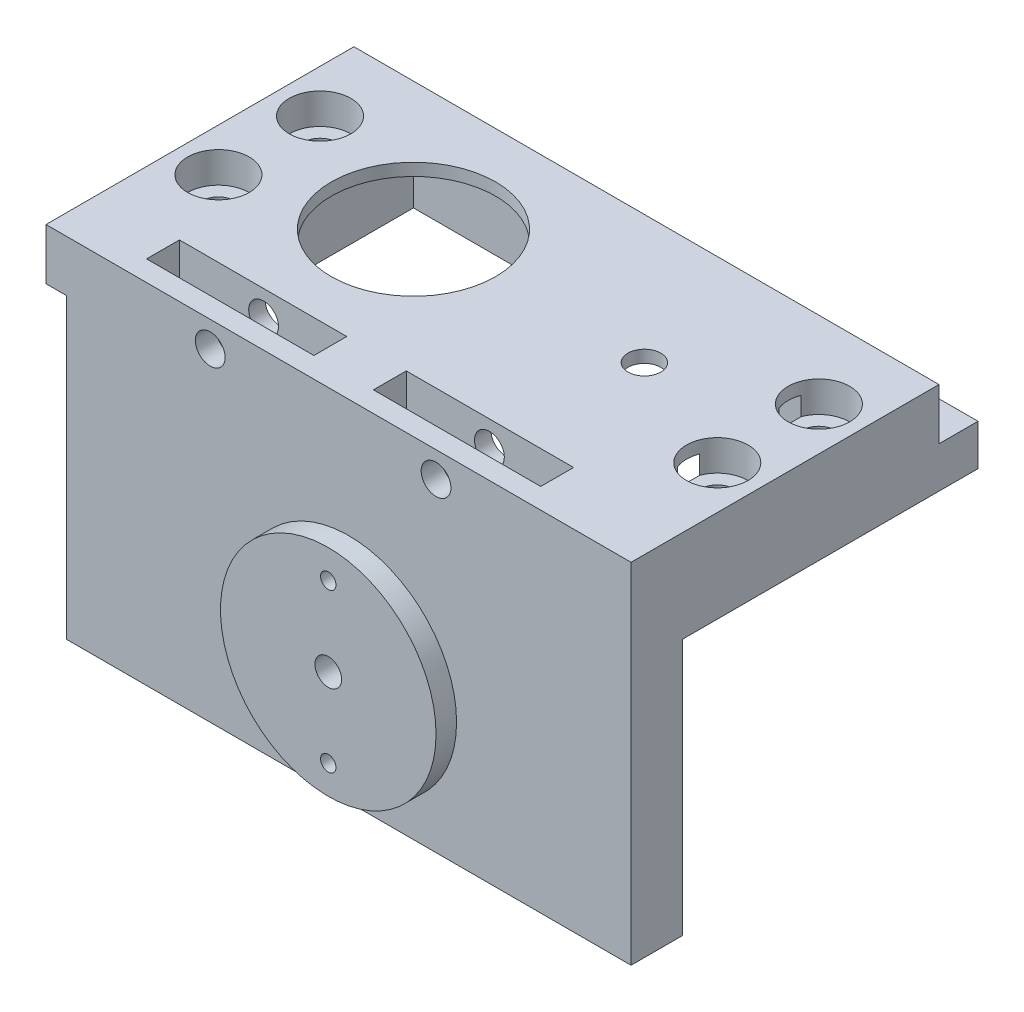
SolidWorks part; units mm, degrees
ref_plane "Front Plane" through (0, 0, 0) normal (0, 0, 1) x (1, 0, 0)
ref_plane "Top Plane" through (0, 0, 0) normal (0, 1, 0) x (1, 0, 0)
ref_plane "Right Plane" through (0, 0, 0) normal (1, 0, 0) x (0, 0, -1)
sketch "Sketch1" plane through (0, 0, 0) normal (0, 1, 0) x (1, 0, 0)
  line L0 (-11.25, 0) -> (11.25, 0)
  line L1 (-25, -12.5) -> (25, -12.5)
  line L2 (-25, -12.5) -> (-25, 12.5)
  line L3 (-25, 12.5) -> (25, 12.5)
  line L4 (25, -12.5) -> (25, 12.5)
  line L5 (-25, -12.5) -> (25, 12.5) construction
  line L6 (-25, 12.5) -> (25, -12.5) construction
  circle A0 centre (-11.25, 0) radius 1.3
  circle A1 centre (11.25, 0) radius 4.5
  point P0 (0, 0)
  point P10 (0, 0)
  dimension "D3" = 2.6
  dimension "D4" = 9
  dimension "D1" = 25
  dimension "D2" = 50
  dimension "D5" = 22.5
extrude "Boss-Extrude1" add sketch "Sketch1" along normal mid plane 5
sketch "Sketch2" plane through (0, 0, 12.5) normal (0, 0, 1) x (1, 0, 0)
  line L0 (-25, 2.5) -> (-25, -2.5) construction
  line L1 (-25, -2.5) -> (25, -2.5)
  line L2 (-25, -2.5) -> (-25, 9.5)
  line L3 (-25, 9.5) -> (25, 9.5)
  line L4 (25, -2.5) -> (25, 9.5)
  line L5 (-25, -2.5) -> (25, -2.5) construction
  dimension "D1" = 50
  dimension "D2" = 12
extrude "Boss-Extrude2" add sketch "Sketch2" along normal blind 3
sketch "Sketch3" plane through (0, 9.5, 0) normal (0, 1, 0) x (1, 0, 0)
  line L0 (-25, -15.5) -> (-25, -12.5) construction
  line L1 (-25, -15.5) -> (25, -15.5)
  line L2 (-25, -15.5) -> (-25, 12.5)
  line L3 (-25, 12.5) -> (25, 12.5)
  line L4 (25, -15.5) -> (25, 12.5)
  line L5 (-25, 12.5) -> (25, 12.5) construction
extrude "Boss-Extrude3" add sketch "Sketch3" along normal blind 3
sketch "Sketch4" plane through (0, 12.5, 0) normal (0, 1, 0) x (1, 0, 0)
  line L0 (11.25, 0) -> (-11.25, 0)
  line L1 (-25, 12.5) -> (25, 12.5) construction
  line L2 (-25, -15.5) -> (-25, 12.5) construction
  circle A0 centre (11.25, 0) radius 1.3
  circle A1 centre (-11.25, 0) radius 1.3
  dimension "D1" = 2.6
  dimension "D2" = 2.6
  dimension "D3" = 11.25
  dimension "D4" = 12.5
  dimension "D5" = 13.75
extrude "Cut-Extrude1" cut sketch "Sketch4" against normal through all
sketch "Sketch5" plane through (0, -2.5, 0) normal (0, -1, 0) x (1, 0, 0)
  line L11 (21.45, -10.3) -> (21.45, 10.2) construction
  line L20 (0.95, 10.2) -> (41.95, 10.2) construction
  line L21 (0.95, 10.2) -> (0.95, -10.3) construction
  line L22 (0.95, -10.3) -> (41.95, -10.3) construction
  line L23 (41.95, 10.2) -> (41.95, -10.3) construction
  line L24 (-5.05, 16.2) -> (47.95, 16.2)
  line L25 (47.95, 16.2) -> (47.95, -16.3)
  line L26 (-5.05, -16.3) -> (47.95, -16.3)
  line L27 (-5.05, 16.2) -> (-5.05, -16.3)
  line L28 (0.45, 10.7) -> (42.45, 10.7)
  line L29 (42.45, 10.7) -> (42.45, -10.8)
  line L30 (0.45, -10.8) -> (42.45, -10.8)
  line L31 (0.45, 10.7) -> (0.45, -10.8)
  circle A5 centre (11.25, 0) radius 7.5 construction
  circle A6 centre (45.75, -5) radius 1.6
  circle A7 centre (45.75, 4.9) radius 1.6
  circle A8 centre (-2.85, 4.9) radius 1.6
  circle A9 centre (-2.85, -5) radius 1.6
  dimension "D4" = 10.3
  dimension "D5" = 10.3
  dimension "D8" = 3.8
  dimension "D9" = 5.3
  dimension "D1" = 15
  dimension "D6" = 3.2
  dimension "D7" = 3.2
  dimension "D2" = 41
  dimension "D3" = 20.5
  dimension "D10" = 5.3
  dimension "D11" = 6
  dimension "D12" = 0.5
extrude "Boss-Extrude4" add sketch "Sketch5" along normal blind 4
sketch "Sketch7" plane through (0, -2.5, 0) normal (0, -1, 0) x (1, 0, 0)
  circle A0 centre (11.25, 0) radius 8
  dimension "D1" = 16
extrude "Cut-Extrude2" cut sketch "Sketch7" against normal up to surface (5 mm away) up to face at (11.25, 2.5, 4.5)
sketch "Sketch8" plane through (0, -2.5, 0) normal (0, -1, 0) x (1, 0, 0)
  line L4 (0.45, 10.7) -> (0.45, -10.8)
  line L5 (0.45, 10.7) -> (0.45, -10.8)
  line L6 (0.45, -10.8) -> (25, -10.8)
  line L7 (25, -10.8) -> (25, 10.7)
  line L11 (25, -10.8) -> (25, 10.7)
  line L12 (0.45, -10.8) -> (25, -10.8)
  line L13 (25, 10.7) -> (0.45, 10.7)
  line L14 (25, 10.7) -> (0.45, 10.7)
  dimension "D1" = 0
extrude "Cut-Extrude3" cut sketch "Sketch8" against normal blind 3.8
sketch "Sketch9" plane through (25, 0, 0) normal (1, 0, 0) x (0, 0, -1)
  line L0 (-12.5, 2.5) -> (-15.5, 2.5)
  line L1 (-15.5, 2.5) -> (-16.2, 2.5)
  line L2 (-16.2, 2.5) -> (-16.2, -2.5)
  line L3 (-16.2, -2.5) -> (-15.5, -2.5)
  line L12 (-10.7, 1.3) -> (10.8, 1.3)
  line L13 (-10.7, -2.5) -> (-10.7, 1.3)
  line L14 (10.8, -2.5) -> (12.5, -2.5)
  line L15 (12.5, -2.5) -> (12.5, 2.5)
  line L16 (12.5, 2.5) -> (-12.5, 2.5)
  line L17 (-12.5, 2.5) -> (-12.5, 9.5)
  line L18 (-12.5, 9.5) -> (12.5, 9.5)
  line L19 (12.5, 9.5) -> (12.5, 12.5)
  line L20 (12.5, 12.5) -> (-15.5, 12.5)
  line L21 (-15.5, 12.5) -> (-15.5, -2.5)
  line L22 (-15.5, -2.5) -> (-10.7, -2.5)
  line L23 (-10.7, -2.5) -> (-10.7, 1.3)
  line L24 (-10.7, 1.3) -> (10.8, 1.3)
  line L26 (10.8, -2.5) -> (12.5, -2.5)
  line L27 (12.5, -2.5) -> (12.5, 2.5)
  line L28 (12.5, 2.5) -> (-12.5, 2.5)
  line L29 (-12.5, 2.5) -> (-12.5, 9.5)
  line L30 (-12.5, 9.5) -> (12.5, 9.5)
  line L31 (12.5, 9.5) -> (12.5, 12.5)
  line L32 (12.5, 12.5) -> (-15.5, 12.5)
  line L33 (-15.5, 12.5) -> (-15.5, -2.5)
  line L34 (-15.5, -2.5) -> (-10.7, -2.5)
  line L40 (10.8, 1.3) -> (10.8, -2.5)
  line L41 (10.8, 1.3) -> (10.8, -2.5)
  dimension "D1" = 0
extrude "Boss-Extrude6" add sketch "Sketch9" along normal up to surface (22.95 mm away) up to face at (47.95, -4.5, -0.05)
sketch "Sketch10" plane through (47.95, 0, 0) normal (1, 0, 0) x (0, 0, -1)
  line L6 (16.3, -2.5) -> (12.5, -2.5)
  line L7 (12.5, -2.5) -> (12.5, 2.5)
  line L8 (12.5, 2.5) -> (-16.2, 2.5)
  line L9 (-16.2, 2.5) -> (-16.2, -6.5)
  line L10 (-16.2, -6.5) -> (16.3, -6.5)
  line L11 (16.3, -6.5) -> (16.3, -2.5)
  line L12 (16.3, -2.5) -> (12.5, -2.5)
  line L13 (12.5, -2.5) -> (12.5, 2.5)
  line L14 (12.5, 2.5) -> (-16.2, 2.5)
  line L15 (-16.2, 2.5) -> (-16.2, -6.5)
  line L16 (-16.2, -6.5) -> (16.3, -6.5)
  line L17 (16.3, -6.5) -> (16.3, -2.5)
  dimension "D1" = 0
extrude "Boss-Extrude7" add sketch "Sketch10" along normal blind 2
sketch "Sketch11" plane through (0, 1.3, 0) normal (0, -1, 0) x (1, 0, 0)
  circle A0 centre (-2.85, 4.9) radius 1.6 construction
  circle A1 centre (-2.85, -5) radius 1.6 construction
  circle A2 centre (45.75, 4.9) radius 1.6 construction
  circle A3 centre (45.75, -5) radius 1.6 construction
  circle A4 centre (-2.85, 4.9) radius 1.6
  circle A5 centre (-2.85, -5) radius 1.6
  circle A6 centre (45.75, 4.9) radius 1.6
  circle A7 centre (45.75, -5) radius 1.6
extrude "Cut-Extrude4" cut sketch "Sketch11" against normal up to surface (1.2 mm away) up to face at (11.25, 2.5, 8)
sketch "Sketch12" plane through (0, 1.3, 0) normal (0, -1, 0) x (1, 0, 0)
  line L0 (49.95, 16.2) -> (49.95, -16.3) construction
  line L1 (42.95, 10.7) -> (49.95, 10.7)
  line L2 (42.95, 10.7) -> (42.95, -10.3)
  line L3 (42.95, -10.3) -> (49.95, -10.3)
  line L4 (49.95, 10.7) -> (49.95, -10.3)
  line L6 (0.45, 10.7) -> (0.45, -10.8) construction
  line L7 (47.95, 10.7) -> (0.45, 10.7) construction
  line L8 (0.45, 10.7) -> (42.45, 10.7) construction
  circle A0 centre (45.75, 4.9) radius 1.6 construction
  circle A1 centre (45.75, -5) radius 1.6 construction
  circle A2 centre (45.75, 4.9) radius 1.6
  circle A3 centre (45.75, -5) radius 1.6
  dimension "D1" = 42.5
  dimension "D2" = 21
extrude "Boss-Extrude8" add sketch "Sketch12" along normal up to surface (7.8 mm away) up to face at (22.45, -6.5, -0.05)
sketch "Sketch13" plane through (25, 0, 0) normal (-1, 0, 0) x (0, 0, 1)
  line L1 (15.5, 2.5) -> (16.2, 2.5)
  line L2 (15.5, 2.5) -> (15.5, -6.5)
  line L3 (15.5, -6.5) -> (16.2, -6.5)
  line L4 (16.2, 2.5) -> (15.5, 2.5)
  line L5 (15.5, 2.5) -> (15.5, -2.5)
  line L6 (15.5, -2.5) -> (16.2, -2.5)
  line L7 (16.2, -2.5) -> (16.2, 2.5)
  line L8 (16.2, 2.5) -> (15.5, 2.5)
  line L9 (15.5, 2.5) -> (15.5, -2.5)
  line L11 (16.2, -2.5) -> (16.2, 2.5)
  line L12 (16.2, 2.5) -> (16.2, -6.5)
  line M5 (16.2, 2.5) -> (15.5, 2.5)
  line M6 (15.5, 2.5) -> (15.5, -2.5)
  line M7 (15.5, -2.5) -> (16.2, -2.5)
  line M8 (16.2, -2.5) -> (16.2, 2.5)
  dimension "D1" = 0
extrude "Cut-Extrude5" cut sketch "Sketch13" against normal through all both and the other way through all contours M8 M5 M6 M7 | L12 L2 L3 M7
sketch "Sketch14" plane through (-25, 0, 0) normal (-1, 0, 0) x (0, 0, 1)
  line L0 (15.5, 12.5) -> (15.5, -2.5) construction
  line L1 (-12.5, 12.5) -> (15.5, 12.5)
  line L2 (-12.5, 12.5) -> (-12.5, 2.5)
  line L3 (-12.5, 2.5) -> (15.5, 2.5)
  line L4 (15.5, 12.5) -> (15.5, 2.5)
  line L5 (12.5, 2.5) -> (-12.5, 2.5) construction
extrude "Cut-Extrude6" cut sketch "Sketch14" against normal through all both and the other way through all
sketch "Sketch15" plane through (0, 2.5, 0) normal (0, 1, 0) x (1, 0, 0)
  circle A0 centre (-2.85, 5) radius 1.6
  circle A1 centre (-2.85, -4.9) radius 1.6
  dimension "D1" = 3.2
  dimension "D2" = 3.2
sketch "Sketch16" plane through (0, 2.5, 0) normal (0, 1, 0) x (1, 0, 0)
  circle A0 centre (-2.85, 5) radius 3
  circle A1 centre (-2.85, -4.9) radius 3
  circle A2 centre (45.75, 5) radius 3
  circle A3 centre (45.75, -4.9) radius 3
  dimension "D1" = 6
  dimension "D2" = 6
  dimension "D3" = 6
  dimension "D4" = 6
extrude "Cut-Extrude8" cut sketch "Sketch16" against normal blind 3
extrude "Cut-Extrude9" cut sketch "Sketch15" against normal up to surface (5 mm away) up to face at (44.45, -2.5, -3.4667)
sketch "Sketch17" plane through (0, 0, 15.5) normal (0, 0, 1) x (1, 0, 0)
  line L1 (49.95, 2.5) -> (-25, 2.5) construction
  line L2 (-5.05, 2.5) -> (0.75, 2.5)
  line L3 (-5.05, 2.5) -> (-5.05, -2.5)
  line L4 (-5.05, -2.5) -> (0.75, -2.5)
  line L5 (0.75, 2.5) -> (0.75, -2.5)
  line L7 (-5.05, 2.5) -> (44.95, 2.5)
  line L8 (22.85, 2.5) -> (17.05, 2.5)
  line L9 (22.85, 2.5) -> (22.85, -2.5)
  line L10 (22.85, -2.5) -> (17.05, -2.5)
  line L11 (17.05, 2.5) -> (17.05, -2.5)
  line L12 (44.95, 2.5) -> (39.15, 2.5)
  line L13 (44.95, 2.5) -> (44.95, -2.5)
  line L14 (44.95, -2.5) -> (39.15, -2.5)
  line L15 (39.15, 2.5) -> (39.15, -2.5)
  line L16 (44.95, -2.5) -> (-5.05, -2.5)
  line L17 (-5.05, -6.5) -> (-5.05, -2.5) construction
  point P17 (19.95, -2.5)
  point P18 (19.95, -2.5)
  line M14 (49.95, 2.5) -> (-25, 2.5)
  dimension "D1" = 5
  dimension "D2" = 5.8
  dimension "D3" = 5.8
  dimension "D4" = 5.8
  dimension "D5" = 50
extrude "Cut-Extrude10" cut sketch "Sketch17" against normal blind 3.2 contours L16 L11 L5 M14 | L16 L15 L7 L9
sketch "Sketch18" plane through (0, 0, 12.3) normal (0, 0, 1) x (1, 0, 0)
  line L3 (39.15, 2.5) -> (22.85, 2.5) construction
  line L4 (17.05, 2.5) -> (0.75, 2.5) construction
  circle A0 centre (8.95, 0) radius 1.45
  circle A1 centre (30.95, 0) radius 1.45
  dimension "D1" = 2.9
  dimension "D2" = 2.9
  dimension "D3" = 22
  dimension "D4" = 14
  dimension "D5" = 2.5
  dimension "D6" = 2.5
  dimension "D7" = 14
extrude "Cut-Extrude11" cut sketch "Sketch18" against normal blind 5
sketch "Sketch19" plane through (0, 2.5, 0) normal (0, 1, 0) x (1, 0, 0)
  line L0 (0.75, -12.3) -> (0.75, -15.5) construction
  line L1 (17.05, -12.3) -> (0.75, -12.3) construction
  circle A0 centre (33.75, 0) radius 1.6
  dimension "D1" = 3.2
  dimension "D2" = 33
  dimension "D3" = 12.3
extrude "Cut-Extrude12" cut sketch "Sketch19" against normal through all both and the other way through all
sketch "Sketch20" plane through (0, 0, 15.5) normal (0, 0, 1) x (1, 0, 0)
  line L0 (0.75, 2.5) -> (-25, 2.5) construction
  line L1 (-25, -2.5) -> (-7.05, -2.5)
  line L2 (-25, -2.5) -> (-25, 2.5)
  line L3 (-25, 2.5) -> (-7.05, 2.5)
  line L4 (-7.05, -2.5) -> (-7.05, 2.5)
  line L6 (-5.05, -6.5) -> (-5.05, -2.5) construction
  dimension "D1" = 2
extrude "Cut-Extrude14" cut sketch "Sketch20" against normal through all both and the other way through all
sketch "Sketch21" plane through (0, 0, 15.5) normal (0, 0, 1) x (1, 0, 0)
  line L0 (0.75, 2.5) -> (39.15, 2.5)
  line L14 (0.75, 2.5) -> (-7.05, 2.5)
  line L15 (-7.05, 2.5) -> (-7.05, -2.5)
  line L16 (-7.05, -2.5) -> (-5.05, -2.5)
  line L17 (-5.05, -2.5) -> (-5.05, -6.5)
  line L18 (-5.05, -6.5) -> (49.95, -6.5)
  line L19 (49.95, -6.5) -> (49.95, 2.5)
  line L20 (49.95, 2.5) -> (39.15, 2.5)
  line L21 (39.15, 2.5) -> (39.15, -2.5)
  line L22 (39.15, -2.5) -> (22.85, -2.5)
  line L23 (22.85, -2.5) -> (22.85, 2.5)
  line L24 (22.85, 2.5) -> (17.05, 2.5)
  line L25 (17.05, 2.5) -> (17.05, -2.5)
  line L26 (17.05, -2.5) -> (0.75, -2.5)
  line L27 (0.75, -2.5) -> (0.75, 2.5)
  line L28 (0.75, 2.5) -> (-7.05, 2.5)
  line L29 (-7.05, 2.5) -> (-7.05, -2.5)
  line L30 (-7.05, -2.5) -> (-5.05, -2.5)
  line L31 (-5.05, -2.5) -> (-5.05, -6.5)
  line L32 (-5.05, -6.5) -> (49.95, -6.5)
  line L33 (49.95, -6.5) -> (49.95, 2.5)
  line L34 (49.95, 2.5) -> (39.15, 2.5)
  line L35 (39.15, 2.5) -> (39.15, -2.5) construction
  line L36 (39.15, -2.5) -> (22.85, -2.5) construction
  line L37 (22.85, -2.5) -> (22.85, 2.5) construction
  line L38 (22.85, 2.5) -> (17.05, 2.5)
  line L39 (17.05, 2.5) -> (17.05, -2.5) construction
  line L40 (17.05, -2.5) -> (0.75, -2.5) construction
  line L41 (0.75, -2.5) -> (0.75, 2.5) construction
  circle A0 centre (8.95, 0) radius 1.45 construction
  circle A1 centre (8.95, 0) radius 1.45
  circle A2 centre (30.95, 0) radius 1.45 construction
  circle A3 centre (30.95, 0) radius 1.45
  line M15 (0.75, 2.5) -> (-7.05, 2.5)
  line M16 (-7.05, 2.5) -> (-7.05, -2.5)
  line M17 (-7.05, -2.5) -> (-5.05, -2.5)
  line M18 (-5.05, -2.5) -> (-5.05, -6.5)
  line M19 (-5.05, -6.5) -> (49.95, -6.5)
  line M20 (49.95, -6.5) -> (49.95, 2.5)
  line M21 (49.95, 2.5) -> (39.15, 2.5)
  line M22 (39.15, 2.5) -> (39.15, -2.5)
  line M23 (39.15, -2.5) -> (22.85, -2.5)
  line M24 (22.85, -2.5) -> (22.85, 2.5)
  line M25 (22.85, 2.5) -> (17.05, 2.5)
  line M26 (17.05, 2.5) -> (17.05, -2.5)
  line M27 (17.05, -2.5) -> (0.75, -2.5)
  line M28 (0.75, -2.5) -> (0.75, 2.5)
  dimension "D1" = 0
extrude "Boss-Extrude11" add sketch "Sketch21" along normal blind 2 contours L0 A1 M28 M27 M26 | M28 M15 M16 M17 M18 M19 M20 M21 M22 M23 M24 M25 M26 M27 | L0 A3 M24 M23 M22
sketch "Sketch22" plane through (0, -6.5, 0) normal (0, -1, 0) x (1, 0, 0)
  line L0 (49.95, 17.5) -> (49.95, -16.3) construction
  line L1 (-5.05, 17.5) -> (49.95, 17.5)
  line L2 (-5.05, 17.5) -> (-5.05, 12.5)
  line L3 (-5.05, 12.5) -> (49.95, 12.5)
  line L4 (49.95, 17.5) -> (49.95, 12.5)
  dimension "D1" = 5
extrude "Boss-Extrude12" add sketch "Sketch22" along normal blind 25
sketch "Sketch23" plane through (0, 0, 17.5) normal (0, 0, 1) x (1, 0, 0)
  line L0 (49.95, -31.5) -> (-5.05, -31.5) construction
  line L1 (-5.05, -2.5) -> (-5.05, -31.5) construction
  circle A0 centre (22.45, -19.5) radius 10.5
  dimension "D3" = 21
  dimension "D1" = 12
  dimension "D2" = 27.5
extrude "Boss-Extrude13" add sketch "Sketch23" along normal blind 2
sketch "Sketch24" plane through (0, 0, 19.5) normal (0, 0, 1) x (1, 0, 0)
  line L0 (19.6233, -19.5) -> (25.912, -19.5) construction
  circle A0 centre (22.45, -19.5) radius 1.3
  circle A1 centre (22.45, -19.5) radius 10.5
  circle A2 centre (22.45, -19.5) radius 10.5
  circle A3 centre (22.45, -11.8) radius 0.75
  circle A4 centre (22.45, -27.2) radius 0.75
  point P8 (0, 0)
  point P11 (0, 0)
  dimension "D2" = 2.6
  dimension "D3" = 1.5
  dimension "D4" = 7.7
  dimension "D1" = 0
extrude "Cut-Extrude16" cut sketch "Sketch24" against normal blind 7 contours A3 | A0 | A4
sketch "Sketch25" plane through (0, 0, 12.5) normal (0, 0, -1) x (-1, 0, 0)
  circle A0 centre (-22.45, -19.5) radius 1.3 construction
  circle A1 centre (-22.45, -19.5) radius 1.3
  circle A2 centre (-22.45, -19.5) radius 2.5
  dimension "D1" = 5
extrude "Cut-Extrude17" cut sketch "Sketch25" against normal blind 4
